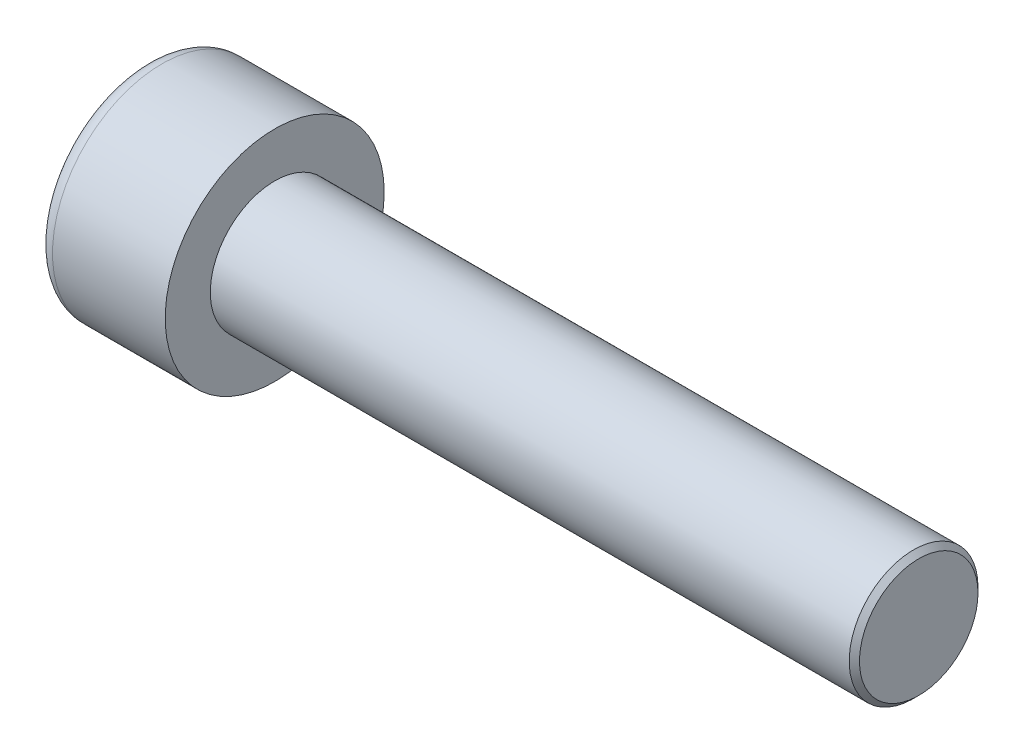
SolidWorks part; units mm, degrees
ref_plane "Front" through (0, 0, 0) normal (0, 0, 1) x (1, 0, 0)
ref_plane "Top" through (0, 0, 0) normal (0, 1, 0) x (1, 0, 0)
ref_plane "Right" through (0, 0, 0) normal (1, 0, 0) x (0, 0, -1)
sketch "Sketch1" plane through (0, 0, 0) normal (1, 0, 0) x (0, 0, -1)
  circle A0 centre (0, 0) radius 4.25
  dimension "dk" = 8.5
extrude "BaseHead" add sketch "Sketch1" along normal blind 5
sketch "Sketch2" plane through (5, 0, 0) normal (1, 0, 0) x (0, 0, -1)
  circle A0 centre (0, 0) radius 2.5
  dimension "d" = 5
extrude "BaseBody" add sketch "Sketch2" along normal blind 25
cosmetic thread "ThreadCosmetic1" parameters "b"=22, "D2"=4.134
sketch "Sketch3" plane through (0, 0, 0) normal (1, 0, 0) x (0, 0, -1)
  line L1 (2.3094, 0) -> (1.1547, 2)
  line L2 (1.1547, 2) -> (-1.1547, 2)
  line L3 (-1.1547, 2) -> (-2.3094, 0)
  line L4 (-2.3094, 0) -> (-1.1547, -2)
  line L5 (-1.1547, -2) -> (1.1547, -2)
  line L6 (1.1547, -2) -> (2.3094, 0)
  circle A0 centre (0, 0) radius 2 construction
  dimension "s" = 4
  dimension "e" = 4.6188
extrude "HexagonSocket" cut sketch "Sketch3" along normal blind 2.5
sketch "Sketch4" plane through (-4.1961, 0.75, 0) normal (0, 0, 1) x (-1, 0, 0)
  line L0 (-6.6961, 2.75) -> (-7.8508, 0.75)
  line L2 (-7.8508, 0.75) -> (-6.6961, 0.75)
  line L3 (-6.6961, 0.75) -> (-6.6961, 2.75)
  line L4 (-5.0351, 0.75) -> (0.839, 0.75) construction
  line L5 (-34.1961, 0.75) -> (-9.1961, 0.75) construction
  line L6 (-9.1961, 0.75) -> (-4.1961, 0.75) construction
  dimension "m" = 60
revolve "Cut-Revolve1" cut sketch "Sketch4" angle 360 about L4
fillet "HeadFillet" [suppressed] radius 0.2
fillet "TopFillet" radius 0.625 1 edges at (0, 0, -4.25)
chamfer "Chamfer1" distance 0.2 angle 45 1 edges at (30, 0, -2.5)
sketch "Sketch5" plane through (0, 0, 0) normal (0, 0, 1) x (1, 0, 0)
  line L0 (29.8, 2.125) -> (30.0165, 2.5)
  line L1 (30.0165, 2.5) -> (30.0165, 2.933)
  line L2 (30.0165, 2.933) -> (29.5835, 2.933)
  line L3 (29.5835, 2.933) -> (29.5835, 2.5)
  line L4 (29.5835, 2.5) -> (29.8, 2.125)
  line L5 (0, 0) -> (7.8886, 0) construction
  line L6 (29.8, -2.5) -> (29.8, 2.5) construction
  dimension "D1" = 5
  dimension "D2" = 0.433
revolve "Cut-Revolve10" [suppressed] cut sketch "Sketch5" angle 360 about L5
pattern_linear "LPattern10" [suppressed] count 42 spacing 0.5196 along (1, 0, 0)
equation "\"r1@TopFillet\" = \"d@Sketch2\" / 8"
equation "\"D1@Chamfer1\" = \"r@HeadFillet\""
equation "\"D1@Sketch5\" = \"d@Sketch2\""
equation "\"D2@Sketch5\" =  ( \"d@Sketch2\" - \"D2@ThreadCosmetic1\" )  / 2"
equation "\"D3@LPattern10\" = \"D2@Sketch5\" * 1.2"
equation "\"D1@LPattern10\" = \"b@ThreadCosmetic1\" / \"D3@LPattern10\""
